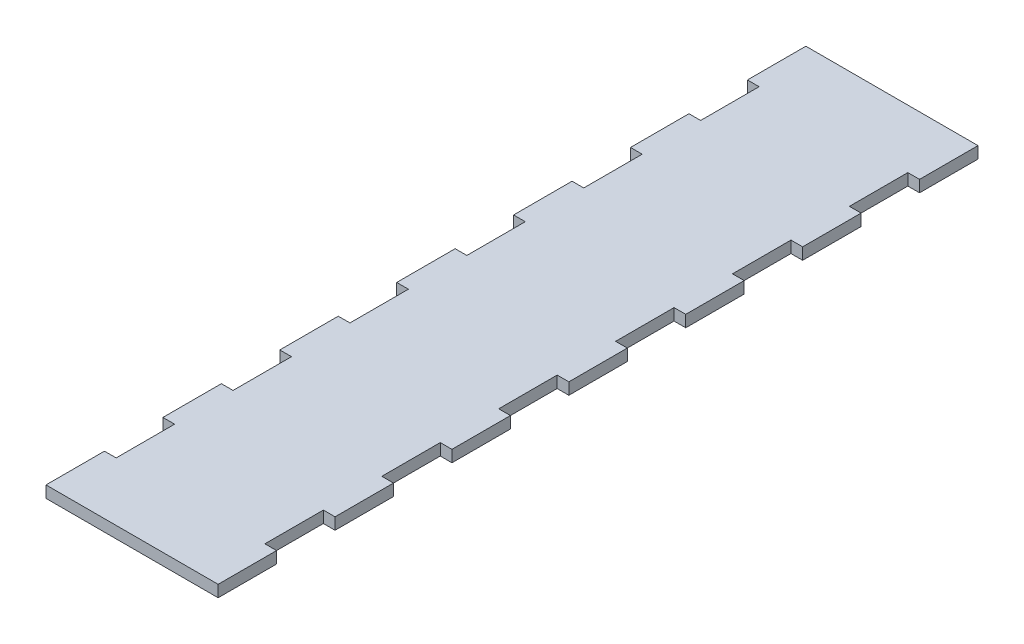
SolidWorks part; units mm, degrees
ref_plane "Спереди" through (0, 0, 0) normal (0, 0, 1) x (1, 0, 0)
ref_plane "Сверху" through (0, 0, 0) normal (0, 1, 0) x (1, 0, 0)
ref_plane "Справа" through (0, 0, 0) normal (1, 0, 0) x (0, 0, -1)
sketch "Эскиз1" plane through (0, 0, 0) normal (0, 1, 0) x (1, 0, 0)
  line L0 (-29.45, -60) -> (-25.45, -60)
  line L1 (29.45, 0) -> (-29.45, 0)
  line L2 (0, 0) -> (0, -260) construction
  line L3 (29.45, -260) -> (-29.45, -260)
  line L4 (-29.45, 0) -> (-29.45, -260)
  line L5 (-29.45, -20) -> (-25.45, -20)
  line L6 (-29.45, -20) -> (-29.45, -40)
  line L7 (-29.45, -40) -> (-25.45, -40)
  line L8 (-25.45, -20) -> (-25.45, -40)
  line L9 (-29.45, -60) -> (-29.45, -80)
  line L10 (-29.45, -80) -> (-25.45, -80)
  line L11 (-25.45, -60) -> (-25.45, -80)
  line L12 (-29.45, -100) -> (-25.45, -100)
  line L13 (-29.45, -100) -> (-29.45, -120)
  line L14 (-29.45, -120) -> (-25.45, -120)
  line L15 (-25.45, -100) -> (-25.45, -120)
  line L16 (-29.45, -140) -> (-25.45, -140)
  line L17 (-29.45, -140) -> (-29.45, -160)
  line L18 (-29.45, -160) -> (-25.45, -160)
  line L19 (-25.45, -140) -> (-25.45, -160)
  line L20 (-29.45, -180) -> (-25.45, -180)
  line L21 (-29.45, -180) -> (-29.45, -200)
  line L22 (-29.45, -200) -> (-25.45, -200)
  line L23 (-25.45, -180) -> (-25.45, -200)
  line L24 (-29.45, -220) -> (-25.45, -220)
  line L25 (-29.45, -220) -> (-29.45, -240)
  line L26 (-29.45, -240) -> (-25.45, -240)
  line L27 (-25.45, -220) -> (-25.45, -240)
  line L28 (25.45, -220) -> (25.45, -240)
  line L29 (29.45, -240) -> (25.45, -240)
  line L30 (29.45, -220) -> (29.45, -240)
  line L31 (29.45, -220) -> (25.45, -220)
  line L32 (25.45, -180) -> (25.45, -200)
  line L33 (29.45, -200) -> (25.45, -200)
  line L34 (29.45, -180) -> (29.45, -200)
  line L35 (29.45, -180) -> (25.45, -180)
  line L36 (25.45, -140) -> (25.45, -160)
  line L37 (29.45, -160) -> (25.45, -160)
  line L38 (29.45, -140) -> (29.45, -160)
  line L39 (29.45, -140) -> (25.45, -140)
  line L40 (25.45, -100) -> (25.45, -120)
  line L41 (29.45, -120) -> (25.45, -120)
  line L42 (29.45, -100) -> (29.45, -120)
  line L43 (29.45, -100) -> (25.45, -100)
  line L44 (25.45, -60) -> (25.45, -80)
  line L45 (29.45, -80) -> (25.45, -80)
  line L46 (29.45, -60) -> (29.45, -80)
  line L47 (25.45, -20) -> (25.45, -40)
  line L48 (29.45, -40) -> (25.45, -40)
  line L49 (29.45, -20) -> (29.45, -40)
  line L50 (29.45, -20) -> (25.45, -20)
  line L51 (29.45, 0) -> (29.45, -260)
  line L52 (29.45, -60) -> (25.45, -60)
  dimension "D1" = 260
  dimension "D2" = 25.45
  dimension "D3" = 4
  dimension "D4" = 20
  dimension "D5" = 20
  dimension "D6" = 6
extrude "Бобышка-Вытянуть1" add sketch "Эскиз1" along normal blind 4 contours L2 L1 L4 L5 L8 L7 L0 L11 L10 L12 L15 L14 L16 L19 L18 L20 L23 L22 L24 L27 L26 L3 | L1 L2 L3 L51 L29 L28 L31 L33 L32 L35 L37 L36 L39 L41 L40 L43 L45 L44 L52 L48 L47 L50
